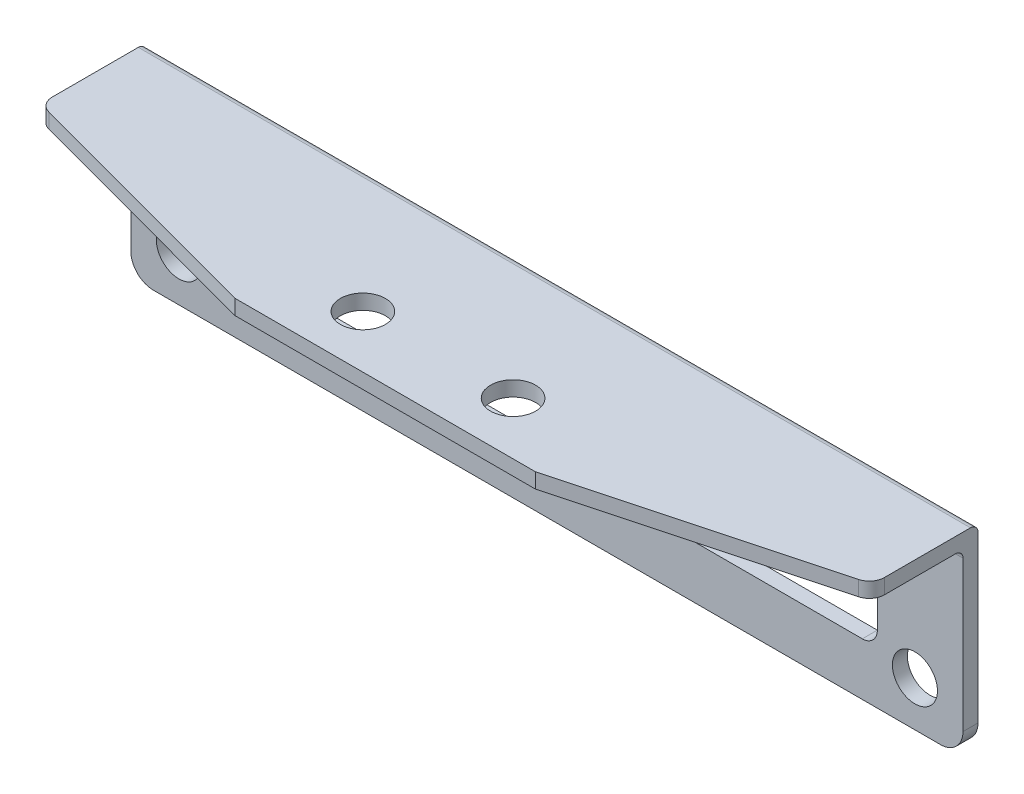
SolidWorks part; units mm, degrees
ref_plane "前视基准面" through (0, 0, 0) normal (0, 0, 1) x (1, 0, 0)
ref_plane "上视基准面" through (0, 0, 0) normal (0, 1, 0) x (1, 0, 0)
ref_plane "右视基准面" through (0, 0, 0) normal (1, 0, 0) x (0, 0, -1)
sketch "草图1" plane through (0, 0, 0) normal (0, 0, 1) x (1, 0, 0)
  line L0 (-27.7, 13) -> (-27.7, 0)
  line L1 (-27.7, 0) -> (27.7, 0)
  line L2 (27.7, 0) -> (27.7, 13)
  line L3 (27.7, 13) -> (-27.7, 13)
  line L5 (-22, 8.3) -> (22, 8.3)
  line L6 (-22, 8.3) -> (-22, 3.5)
  line L7 (0, 0) -> (0, 14.9169) construction
  line L8 (-22, 3.5) -> (22, 3.5)
  line L9 (22, 8.3) -> (22, 3.5)
  line L10 (-22, 8.3) -> (22, 3.5) construction
  line L11 (-22, 3.5) -> (22, 8.3) construction
  circle A2 centre (-24.5, 3) radius 1.5
  circle A3 centre (24.5, 3) radius 1.5
  circle A4 centre (-24.5, 3) radius 2.5 construction
  point P2 (0, 5.9)
  dimension "D1" = 3
  dimension "D2" = 3
  dimension "D10" = 5
  dimension "D3" = 49
  dimension "D4" = 10
  dimension "D5" = 55.4
  dimension "D6" = 44
  dimension "D7" = 4.8
  dimension "D8" = 3.5
  dimension "D9" = 13
extrude "凸台-拉伸1" add sketch "草图1" along normal blind 1
sketch "草图2" plane through (0, 0, 1) normal (0, 0, 1) x (1, 0, 0)
  line L0 (27.7, 13) -> (-27.7, 13) construction
  line L1 (27.7, 13) -> (-27.7, 13)
  line L2 (27.7, 12) -> (-27.7, 12)
  line L3 (-27.7, 13) -> (-27.7, 12)
  line L4 (27.7, 13) -> (27.7, 12)
  dimension "D1" = 1
extrude "凸台-拉伸2" add sketch "草图2" along normal blind 10.75
sketch "草图3" plane through (0, 12, 0) normal (0, -1, 0) x (1, 0, 0)
  line L0 (-27.7, 11.75) -> (-27.7, 1) construction
  line L1 (27.7, 11.75) -> (27.7, 1) construction
  line L2 (-27.7, 11.75) -> (-27.7, 7)
  line L3 (27.7, 11.75) -> (27.7, 7)
  line L4 (-10, 11.75) -> (-27.7, 7)
  line L5 (-27.7, 11.75) -> (27.7, 11.75) construction
  line L6 (0, 0) -> (0, 16.8501) construction
  line L7 (10, 11.75) -> (27.7, 7)
  line L8 (-27.7, 11.75) -> (-10, 11.75)
  line L9 (10, 11.75) -> (27.7, 11.75)
  line L10 (-27.7, 1) -> (27.7, 1) construction
  dimension "D1" = 20
  dimension "D2" = 6
extrude "切除-拉伸1" cut sketch "草图3" against normal through all
sketch "草图4" plane through (0, 12, 0) normal (0, -1, 0) x (1, 0, 0)
  line L0 (-14.9845, 8.25) -> (10.8142, 8.25) construction
  line L1 (-10, 11.75) -> (10, 11.75) construction
  line L2 (0, 0) -> (0, 12.2171) construction
  circle A0 centre (-5, 8.25) radius 1.5
  circle A1 centre (5, 8.25) radius 1.5
  dimension "D3" = 3
  dimension "D4" = 3
  dimension "D1" = 3.5
  dimension "D2" = 10
extrude "切除-拉伸2" cut sketch "草图4" against normal through all
fillet "圆角1" radius 0.5 2 edges at (0, 13, 0)
fillet "圆角2" radius 1 4 edges at (22, 3.5, 0.5) (22, 8.3, 0.5) (-22, 3.5, 0.5) (-22, 8.3, 0.5)
fillet "圆角3" radius 1.5 2 edges at (27.7, 0, 0.5) (-27.7, 0, 0.5)
fillet "圆角4" radius 1 2 edges at (-27.7, 12.5, 7) (27.7, 12.5, 7)
